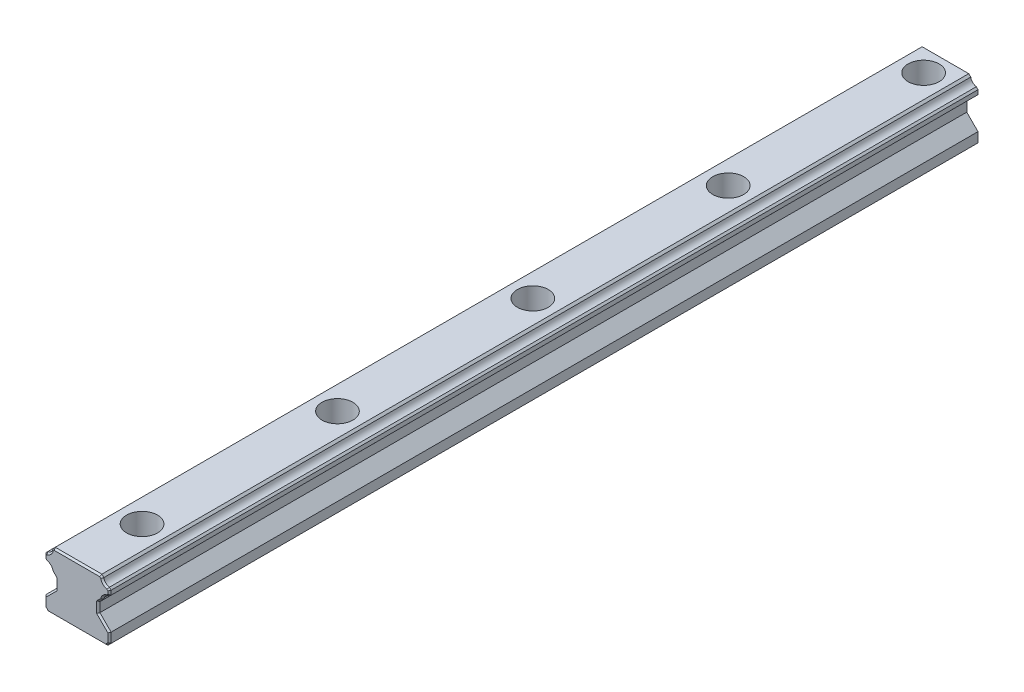
SolidWorks part; units mm, degrees
ref_plane "Front Plane" through (0, 0, 0) normal (0, 0, 1) x (1, 0, 0)
ref_plane "Top Plane" through (0, 0, 0) normal (0, 1, 0) x (1, 0, 0)
ref_plane "Right Plane" through (0, 0, 0) normal (1, 0, 0) x (0, 0, -1)
sketch "Sketch1" plane through (-20, 0, 0) normal (0, 0, 1) x (1, 0, 0)
  line L0 (10, -4.9999) -> (10, -8)
  line L1 (10, -8) -> (11, -9)
  line L2 (11, -9) -> (20, -9)
  line L3 (17, 9) -> (23, 9)
  line L5 (26.55, -1.55) -> (30, -4.9999)
  line L6 (26.55, 1.3792) -> (26.55, -1.55)
  line L7 (27.7679, 2.5951) -> (26.55, 1.3792)
  line L8 (30, 4.8292) -> (29.4727, 4.3144)
  line L9 (30, 6.16) -> (30, 4.8292)
  line L10 (29.4727, 6.6874) -> (30, 6.16)
  line L11 (27.16, 9) -> (27.7679, 8.3921)
  line L13 (29, -9) -> (20, -9)
  line L14 (30, -8) -> (29, -9)
  line L15 (30, -4.9999) -> (30, -8)
  line L16 (27.16, 9) -> (12.84, 9)
  line L17 (12.84, 9) -> (12.2321, 8.3921)
  line L18 (10.5273, 6.6874) -> (10, 6.16)
  line L19 (10, 6.16) -> (10, 4.8292)
  line L20 (10, 4.8292) -> (10.5273, 4.3144)
  line L21 (12.2321, 2.5951) -> (13.45, 1.3792)
  line L22 (13.45, 1.3792) -> (13.45, -1.55)
  line L23 (13.45, -1.55) -> (10, -4.9999)
  line L25 (20, -9) -> (20, 9) construction
  arc A0 (29.4727, 4.3144) -> (27.7679, 2.5951) centre (29.8039, 2.2812) ccw
  arc A1 (27.7679, 8.3921) -> (29.4727, 6.6874) centre (29.8015, 8.7209) ccw
  arc A2 (12.2321, 8.3921) -> (10.5273, 6.6874) centre (10.1985, 8.7209) cw
  arc A3 (10.5273, 4.3144) -> (12.2321, 2.5951) centre (10.1961, 2.2812) cw
  point P3 (20, 0.5)
  point P37 (20, 0)
  point P42 (20, 9)
  dimension "D17" = 2.06
  dimension "Rail Width" = 20
  dimension "D2" = 1
  dimension "D3" = 1
  dimension "D4" = 6
  dimension "D7" = 18
  dimension "D8" = 4.0001
  dimension "D9" = 10.55
  dimension "D10" = 13.1001
  dimension "D11" = 15.5359
  dimension "D12" = 0.6079
  dimension "D13" = 0.6079
  dimension "D15" = 0.5273
  dimension "D16" = 0.5273
  dimension "D18" = 1.2159
  dimension "D19" = 0.5148
  dimension "D20" = 6.4049
  dimension "D21" = 2.84
  dimension "D22" = 4.1708
  dimension "Rail Height" = 18
  dimension "Mounting Hole Dpeth" = 8.5
sketch "Sketch2" plane through (0, 0, 0) normal (1, 0, 0) x (0, 0, -1)
  line L0 (-120, 9) -> (-115.25, 9)
  line L1 (-115.25, 9) -> (-115.25, 0.5)
  line L2 (-115.25, 0.5) -> (-117, 0.5)
  line L3 (-117, 0.5) -> (-117, -9)
  line L4 (-117, -9) -> (-120, -9)
  line L5 (-120, -9) -> (-120, 9) construction
  line L6 (-120, -9) -> (-120, 9) construction
  line L7 (50, 0) -> (-50, 0)
  line L9 (-120, 9) -> (-120, -9)
  line L10 (140, 0) -> (-140, 0) construction
  point P6 (0, 0)
  point P7 (-120, 0)
  point P8 (60, 0)
  point P11 (0, 0)
  point P12 (-60, 0)
  point P14 (-50, 0)
  point P21 (0, 0)
  point P22 (50, 0)
  point P24 (120, 0)
  point P35 (50, -1)
  dimension "D1" = 9.5
  dimension "D3" = 6
  dimension "Rail Length" = 280
  dimension "Mounting Hole Center-to-End" = 20
  dimension "Mounting Hole Center-to-Center" = 60
  dimension "D2" = 90
  dimension "D4" = 1
  dimension "Number of Mounting Holes" = 5
sketch "Sketch3" plane through (0, 0, 0) normal (0, 0, 1) x (1, 0, 0)
  line L0 (-3, 9) -> (3, 9) construction
  line L3 (-3, 9) -> (3, 9)
  line L21 (0, -9) -> (9, -9)
  line L22 (9, -9) -> (10, -8)
  line L23 (10, -8) -> (10, -4.9999)
  line L24 (10, -4.9999) -> (6.55, -1.55)
  line L25 (6.55, -1.55) -> (6.55, 1.3792)
  line L26 (6.55, 1.3792) -> (7.7679, 2.5951)
  line L27 (9.4727, 4.3144) -> (10, 4.8292)
  line L28 (10, 4.8292) -> (10, 6.16)
  line L29 (10, 6.16) -> (9.4727, 6.6874)
  line L30 (7.7679, 8.3921) -> (7.16, 9)
  line L31 (7.16, 9) -> (-7.16, 9)
  line L32 (-7.16, 9) -> (-7.7679, 8.3921)
  line L33 (-9.4727, 6.6874) -> (-10, 6.16)
  line L34 (-10, 6.16) -> (-10, 4.8292)
  line L35 (-10, 4.8292) -> (-9.4727, 4.3144)
  line L36 (-7.7679, 2.5951) -> (-6.55, 1.3792)
  line L37 (-6.55, 1.3792) -> (-6.55, -1.55)
  line L38 (-6.55, -1.55) -> (-10, -4.9999)
  line L39 (-10, -4.9999) -> (-10, -8)
  line L40 (-10, -8) -> (-9, -9)
  line L41 (-9, -9) -> (0, -9)
  line L42 (0, -9) -> (9, -9)
  line L43 (9, -9) -> (10, -8)
  line L44 (10, -8) -> (10, -4.9999)
  line L45 (10, -4.9999) -> (6.55, -1.55)
  line L46 (6.55, -1.55) -> (6.55, 1.3792)
  line L47 (6.55, 1.3792) -> (7.7679, 2.5951)
  line L48 (9.4727, 4.3144) -> (10, 4.8292)
  line L49 (10, 4.8292) -> (10, 6.16)
  line L50 (10, 6.16) -> (9.4727, 6.6874)
  line L51 (7.7679, 8.3921) -> (7.16, 9)
  line L52 (7.16, 9) -> (-7.16, 9)
  line L53 (-7.16, 9) -> (-7.7679, 8.3921)
  line L54 (-9.4727, 6.6874) -> (-10, 6.16)
  line L55 (-10, 6.16) -> (-10, 4.8292)
  line L56 (-10, 4.8292) -> (-9.4727, 4.3144)
  line L57 (-7.7679, 2.5951) -> (-6.55, 1.3792)
  line L58 (-6.55, 1.3792) -> (-6.55, -1.55)
  line L59 (-6.55, -1.55) -> (-10, -4.9999)
  line L60 (-10, -4.9999) -> (-10, -8)
  line L61 (-10, -8) -> (-9, -9)
  line L62 (-9, -9) -> (0, -9)
  arc A4 (9.4727, 4.3144) -> (7.7679, 2.5951) centre (9.8039, 2.2812) ccw
  arc A5 (7.7679, 8.3921) -> (9.4727, 6.6874) centre (9.8015, 8.7209) ccw
  arc A6 (-9.4727, 6.6874) -> (-7.7679, 8.3921) centre (-9.8015, 8.7209) ccw
  arc A7 (-7.7679, 2.5951) -> (-9.4727, 4.3144) centre (-9.8039, 2.2812) ccw
  arc A8 (9.4727, 4.3144) -> (7.7679, 2.5951) centre (9.8039, 2.2812) ccw
  arc A9 (7.7679, 8.3921) -> (9.4727, 6.6874) centre (9.8015, 8.7209) ccw
  arc A10 (-9.4727, 6.6874) -> (-7.7679, 8.3921) centre (-9.8015, 8.7209) ccw
  arc A11 (-7.7679, 2.5951) -> (-9.4727, 4.3144) centre (-9.8039, 2.2812) ccw
  dimension "D1" = 0
extrude "Boss-Extrude1" add sketch "Sketch3" along normal up to vertex (140 mm away) and the other way up to vertex (140 mm away) contours A11 L57 L58 L59 L60 L61 L62 L42 L43 L44 L45 L46 L47 A8 L48 L49 L50 A9 L51 L52 L3 L53 A10 L54 L55 L56 up to point (0, 0, 140) other way up to point (0, 0, -140)
sketch "Sketch4" plane through (0, 0, 0) normal (1, 0, 0) x (0, 0, -1)
  line L6 (-115.25, 9) -> (-120, 9)
  line L7 (-115.25, 0.5) -> (-115.25, 9)
  line L8 (-117, 0.5) -> (-115.25, 0.5)
  line L9 (-117, -9) -> (-117, 0.5)
  line L10 (-120, -9) -> (-117, -9)
  line L11 (-120, 9) -> (-120, -9)
  line L12 (-115.25, 9) -> (-120, 9)
  line L13 (-115.25, 0.5) -> (-115.25, 9)
  line L14 (-117, 0.5) -> (-115.25, 0.5)
  line L15 (-117, -9) -> (-117, 0.5)
  line L16 (-120, -9) -> (-117, -9)
  line L17 (-120, 9) -> (-120, -9)
  dimension "D1" = 0
revolve "Cut-Revolve1" cut sketch "Sketch4" angle 360 about L17
pattern_linear "LPattern2" count 5 spacing 60 along (0, 0, -1) of "Cut-Revolve1"
sketch "Sketch5" plane through (0, 0, 0) normal (0, 1, 0) x (1, 0, 0)
  line L0 (3, -120) -> (0, -120) construction
  line L1 (0, -120) -> (2.1213, -117.8787) construction
  circle A1 centre (0, -120) radius 3 construction
  circle A2 centre (0, -120) radius 3 construction
  point P3 (0, -123)
  point P4 (-3, -120)
  point P6 (3, -120)
  point P7 (2.1213, -117.8787)
  dimension "D1" = 45
sketch "Sketch6" plane through (0, 0, 0) normal (0, 0, 1) x (1, 0, 0)
  line L0 (4.75, 9) -> (-4.75, 9) construction
  line L1 (3, 0.5) -> (-3, 0.5) construction
  line L2 (4.75, 9) -> (-4.75, 9) construction
  line L3 (3, 0.5) -> (-3, 0.5) construction
  line L4 (-4.75, 9) -> (-4.75, 0.5)
  line L5 (-4.75, 0.5) -> (-3, 0.5)
  line L6 (4.75, 9) -> (4.75, 0.5)
  line L7 (4.75, 0.5) -> (3, 0.5)
  line L8 (3, 0.5) -> (3, -9)
  line L9 (-9, -9) -> (9, -9) construction
  line L10 (-3, 0.5) -> (-3, -9)
chamfer "Chamfer1" distance 0.5 angle 45 48 edges at (-7.159, 1.9872, -140) (-6.55, -0.0854, -140) (-8.275, -3.275, -140) (-10, -6.5, -140) (-9.5, -8.5, -140) (0, -9, -140) (9.5, -8.5, -140) (10, -6.5, -140) (8.275, -3.275, -140) (6.55, -0.0854, -140) (7.159, 1.9872, -140) (8.3411, 3.7316, -140) (9.7363, 4.5718, -140) (10, 5.4946, -140) (9.7363, 6.4237, -140) (8.3449, 7.2643, -140) (7.464, 8.6961, -140) (0, 9, -140) (-7.464, 8.6961, -140) (-8.3449, 7.2643, -140) (-9.7363, 6.4237, -140) (-10, 5.4946, -140) (-9.7363, 4.5718, -140) (-8.3411, 3.7316, -140) (-9.7363, 4.5718, 140) (-10, 5.4946, 140) (-9.7363, 6.4237, 140) (-8.3449, 7.2643, 140) (-7.464, 8.6961, 140) (0, 9, 140) (7.464, 8.6961, 140) (8.3449, 7.2643, 140) (9.7363, 6.4237, 140) (10, 5.4946, 140) (9.7363, 4.5718, 140) (8.3411, 3.7316, 140) (7.159, 1.9872, 140) (6.55, -0.0854, 140) (8.275, -3.275, 140) (10, -6.5, 140) (9.5, -8.5, 140) (0, -9, 140) (-9.5, -8.5, 140) (-10, -6.5, 140) (-8.275, -3.275, 140) (-6.55, -0.0854, 140) (-7.159, 1.9872, 140) (-8.3411, 3.7316, 140)
sketch "Sketch7" plane through (0, -9, 0) normal (0, -1, 0) x (1, 0, 0)
  line L0 (15.69, -126.7) -> (-26.1609, -126.7)
  line L1 (-9.4958, -126.7) -> (-14.3167, -126.7) construction
extrude "Cut-Extrude1" cut sketch "Sketch7" against normal through all and the other way through all
equation "\"D3@LPattern2\"=\"Mounting Hole Center-to-Center@Sketch2\""
equation "\"D1@LPattern2\"=\"Number of Mounting Holes@Sketch2\""
